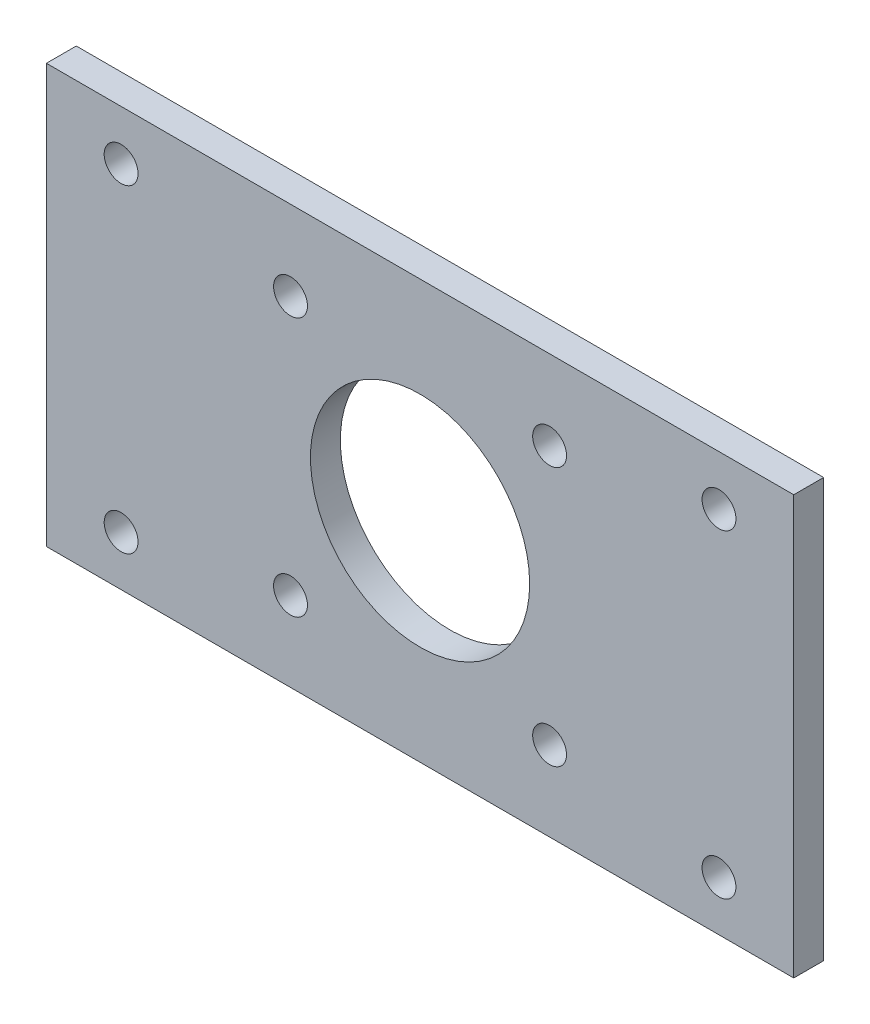
SolidWorks part; units mm, degrees
ref_plane "Front Plane" through (0, 0, 0) normal (0, 0, 1) x (1, 0, 0)
ref_plane "Top Plane" through (0, 0, 0) normal (0, 1, 0) x (1, 0, 0)
ref_plane "Right Plane" through (0, 0, 0) normal (1, 0, 0) x (0, 0, -1)
sketch "Sketch1" plane through (0, 0, 0) normal (0, 0, 1) x (1, 0, 0)
  line L0 (-37.5, -21) -> (37.5, 21) construction
  line L1 (-37.5, -21) -> (37.5, -21)
  line L2 (-37.5, -21) -> (-37.5, 21)
  line L3 (-37.5, 21) -> (37.5, 21)
  line L4 (37.5, -21) -> (37.5, 21)
  line L5 (37.5, -21) -> (-37.5, 21) construction
  dimension "D1" = 75
  dimension "D2" = 42
extrude "Boss-Extrude1" add sketch "Sketch1" along normal blind 3
sketch "Sketch2" plane through (0, 0, 3) normal (0, 0, 1) x (1, 0, 0)
  circle A0 centre (0, 0) radius 11
  dimension "D1" = 22
extrude "Cut-Extrude1" cut sketch "Sketch2" against normal through all
hole_wizard "M3 Clearance Hole1" positions "Sketch4" profile "Sketch3" hole size "M3" standard "ANSI Metric" end condition through all
sketch "Sketch4" plane through (0, 0, 3) normal (0, 0, 1) x (1, 0, 0)
  line L0 (-13, -13) -> (13, -13) construction
  line L1 (13, -13) -> (13, 13) construction
  line L2 (13, 13) -> (-13, -13) construction
  line L3 (-13, -13) -> (-13, 13) construction
  line L4 (-13, 13) -> (13, -13) construction
  point P0 (-13, -13)
  point P2 (13, -13)
  point P4 (13, 13)
  point P6 (-13, 13)
  dimension "D1" = 26
sketch "Sketch3" plane through (-13, -13, 3) normal (1, 0, 0) x (0, -1, 0)
  line L0 (0, 0) -> (0, 3)
  line L1 (0, 3) -> (1.7, 3)
  line L2 (1.7, 3) -> (1.7, 0)
  line L5 (1.7, 0) -> (0, 0)
  line L11 (0, -6.35) -> (0, 107.95) construction
  dimension "Thru Hole Dia." = 3.4
  dimension "Thru Hole Depth" = 3
hole_wizard "M3 Clearance Hole2" positions "Sketch6" profile "Sketch5" hole size "M3" standard "ANSI Metric" end condition through all
sketch "Sketch6" plane through (0, 0, 3) normal (0, 0, 1) x (1, 0, 0)
  line L0 (-30, -16) -> (-30, 16) construction
  line L2 (30, -16) -> (30, 16) construction
  line L4 (-30, 0) -> (30, 0) construction
  line L6 (37.5, 21) -> (-37.5, 21) construction
  line L7 (-37.5, 21) -> (-37.5, -21) construction
  point P0 (-30, -16)
  point P2 (-30, 16)
  point P4 (30, -16)
  point P6 (30, 16)
  dimension "D1" = 5
  dimension "D2" = 7.5
sketch "Sketch5" plane through (-30, -16, 3) normal (1, 0, 0) x (0, -1, 0)
  line L0 (0, 0) -> (0, 3)
  line L1 (0, 3) -> (1.7, 3)
  line L2 (1.7, 3) -> (1.7, 0)
  line L5 (1.7, 0) -> (0, 0)
  line L11 (0, -6.35) -> (0, 107.95) construction
  dimension "Thru Hole Dia." = 3.4
  dimension "Thru Hole Depth" = 3
